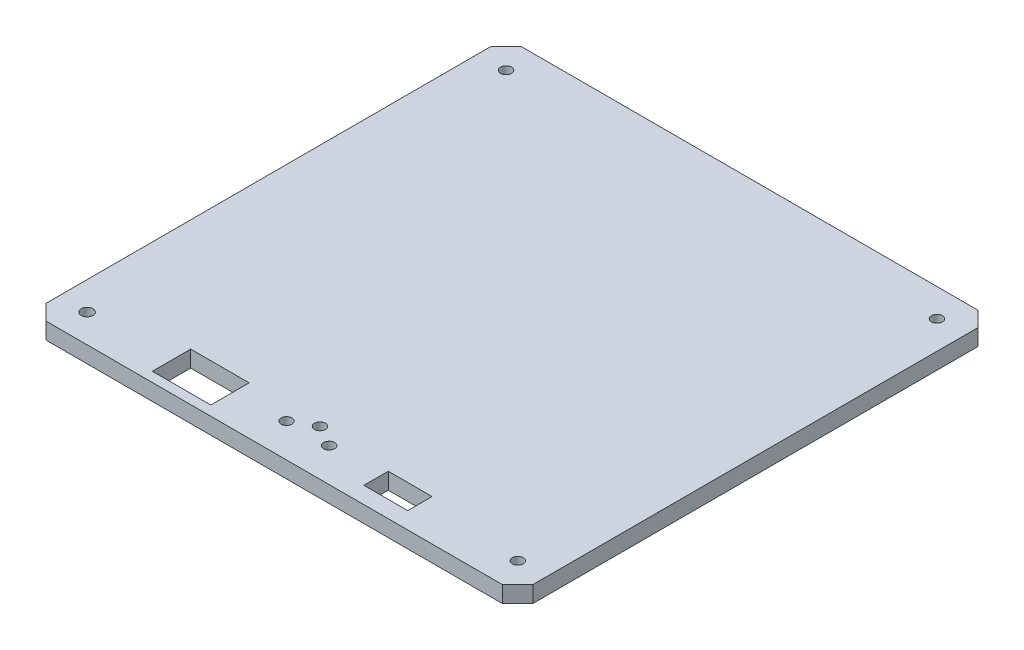
SolidWorks part; units mm, degrees
ref_plane "Front Plane" through (0, 0, 0) normal (0, 0, 1) x (1, 0, 0)
ref_plane "Top Plane" through (0, 0, 0) normal (0, 1, 0) x (1, 0, 0)
ref_plane "Right Plane" through (0, 0, 0) normal (1, 0, 0) x (0, 0, -1)
sketch "Sketch1" plane through (0, 0, 0) normal (0, 1, 0) x (1, 0, 0)
  line L1 (-75.184, -75.184) -> (75.184, -75.184)
  line L2 (-75.184, -75.184) -> (-75.184, 75.184)
  line L3 (-75.184, 75.184) -> (75.184, 75.184)
  line L4 (75.184, -75.184) -> (75.184, 75.184)
  line L5 (-75.184, -75.184) -> (75.184, 75.184) construction
  line L6 (-75.184, 75.184) -> (75.184, -75.184) construction
  point P0 (0, 0)
  dimension "D1" = 150.368
  dimension "D2" = 150.368
extrude "Boss-Extrude1" add sketch "Sketch1" along normal blind 6.858
sketch "Sketch2" plane through (0, 6.858, 0) normal (0, 1, 0) x (1, 0, 0)
  line L1 (-101.6, -99.187) -> (101.6, -99.187)
  line L2 (-101.6, -99.187) -> (-101.6, 99.187)
  line L3 (-101.6, 99.187) -> (101.6, 99.187)
  line L4 (101.6, -99.187) -> (101.6, 99.187)
  line L5 (-101.6, -99.187) -> (101.6, 99.187) construction
  line L6 (-101.6, 99.187) -> (101.6, -99.187) construction
  point P0 (0, 0)
  dimension "D1" = 203.2
  dimension "D2" = 198.374
extrude "Boss-Extrude2" add sketch "Sketch2" against normal blind 6.858
sketch "Sketch4" plane through (0, 6.858, 0) normal (0, 1, 0) x (1, 0, 0)
  circle A0 centre (0.0008, -80.0467) radius 2.286
  dimension "D1" = 4.572
sketch "Sketch5" plane through (0, 6.858, 0) normal (0, 1, 0) x (1, 0, 0)
  circle A0 centre (-8.8892, -85.1267) radius 2.286
  circle A1 centre (8.8908, -85.1267) radius 2.286
extrude "Cut-Extrude2" cut sketch "Sketch5" against normal up to surface (6.858 mm away) up to face at (0, 0, 0)
sketch "Sketch6" plane through (0, 0, 0) normal (0, -1, 0) x (-1, 0, 0)
  line L0 (12.6992, -83.8567) -> (12.6992, -86.3967) construction
  line L1 (-30.4808, -82.0316) -> (-48.7688, -82.0316)
  line L2 (-30.4808, -82.0316) -> (-30.4808, -92.1916)
  line L3 (-30.4808, -92.1916) -> (-48.7688, -92.1916)
  line L4 (-48.7688, -82.0316) -> (-48.7688, -92.1916)
  line L5 (-30.4808, -82.0316) -> (-48.7688, -92.1916) construction
  line L6 (-30.4808, -92.1916) -> (-48.7688, -82.0316) construction
  line L7 (54.8632, -79.1106) -> (30.4792, -79.1106)
  line L8 (54.8632, -79.1106) -> (54.8632, -95.1126)
  line L9 (54.8632, -95.1126) -> (30.4792, -95.1126)
  line L10 (30.4792, -79.1106) -> (30.4792, -95.1126)
  line L11 (54.8632, -79.1106) -> (30.4792, -95.1126) construction
  line L12 (54.8632, -95.1126) -> (30.4792, -79.1106) construction
  line L13 (-12.7008, -86.3967) -> (-12.7008, -83.8567) construction
  point P0 (-39.6248, -87.1116)
  point P5 (42.6712, -87.1116)
  point P10 (42.814, -87.1116)
  point P11 (-38.8513, -87.1116)
  dimension "D1" = 10.16
  dimension "D2" = 18.288
  dimension "D3" = 24.384
  dimension "D4" = 16.002
  dimension "D5" = 17.78
  dimension "D6" = 17.78
extrude "Cut-Extrude3" cut sketch "Sketch6" against normal up to surface (6.858 mm away) up to face at (-8.8892, 6.858, 87.4127)
sketch "Sketch7" plane through (0, 6.858, 0) normal (0, 1, 0) x (1, 0, 0)
  line L0 (-101.6, 99.187) -> (-101.6, 93.0071)
  line L1 (-101.6, 99.187) -> (-101.6, -99.187) construction
  line L2 (-101.6, 93.0071) -> (-95.3395, 99.187)
  line L3 (101.6, 99.187) -> (-101.6, 99.187) construction
  line L4 (-95.2492, 99.2773) -> (-101.5992, 92.9273) construction
  line L5 (-95.3395, 99.187) -> (-101.6, 99.187)
  line L6 (101.6, 99.187) -> (95.3411, 99.187)
  line L7 (101.6008, 92.9273) -> (95.2508, 99.2773) construction
  line L8 (95.3411, 99.187) -> (101.6, 92.9281)
  line L9 (101.6, -99.187) -> (101.6, 99.187) construction
  line L10 (101.6, 92.9281) -> (101.6, 99.187)
  line L11 (101.6, -99.187) -> (95.3411, -99.187)
  line L12 (-101.6, -99.187) -> (101.6, -99.187) construction
  line L13 (95.3411, -99.187) -> (101.6, -92.7475)
  line L14 (95.2508, -99.0967) -> (101.6008, -92.7467) construction
  line L15 (101.6, -92.7475) -> (101.6, -99.187)
  line L16 (-101.6, -99.187) -> (-101.6, -92.7475)
  line L19 (-101.6, -92.7475) -> (-95.18, -99.187)
  line L20 (-101.6, -99.187) -> (-95.18, -99.187)
  point P32 (-95.18, -99.187)
  point P35 (-95.2492, -99.0967)
  point P41 (-95.18, -99.1735)
  line M12 (101.6, -99.187) -> (101.6, 99.187)
  line M15 (-101.6, -99.187) -> (101.6, -99.187)
sketch "Sketch8" plane through (0, 6.858, 0) normal (0, 1, 0) x (1, 0, 0)
  line L0 (-54.8632, -79.1106) -> (-54.8632, -95.1126) construction
  line L1 (-54.8632, -95.1126) -> (-30.4792, -95.1126) construction
  circle A0 centre (-89.8618, -87.3593) radius 2.4503
  circle A1 centre (89.8635, -87.3593) radius 2.286
  circle A2 centre (89.8635, 87.54) radius 2.286
  circle A3 centre (-89.8618, 87.4488) radius 2.286
  dimension "D1" = 4.9006
  dimension "D2" = 4.572
  dimension "D3" = 144.7267
  dimension "D4" = 34.9987
  dimension "D5" = 7.7533
  dimension "D6" = 182.5615
  dimension "D7" = 182.6526
extrude "Cut-Extrude8" cut sketch "Sketch8" against normal up to surface (6.858 mm away) up to face at (39.6248, 0, 87.1116)
extrude "Cut-Extrude10" cut sketch "Sketch7" against normal up to surface (6.858 mm away) contours L13 M15 M12 | L5 L0 L2 | L10 L6 L8 | L19 L20 L16 up to face at (-89.8618, 0, -89.7348)
sketch "Sketch9" plane through (0, 0, 0) normal (0, -1, 0) x (-1, 0, 0)
  line L1 (75.184, 78.8843) -> (-75.184, 78.8843)
  line L2 (75.184, 78.8843) -> (75.184, -71.4837)
  line L3 (75.184, -71.4837) -> (-75.184, -71.4837)
  line L4 (-75.184, 78.8843) -> (-75.184, -71.4837)
  line L5 (75.184, 78.8843) -> (-75.184, -71.4837) construction
  line L6 (75.184, -71.4837) -> (-75.184, 78.8843) construction
  point P0 (0, 13.6102)
  point P7 (0, 13.6102)
  dimension "D1" = 150.368
extrude "Cut-Extrude11" cut sketch "Sketch9" against normal blind 5.08
extrude "Cut-Extrude12" cut sketch "Sketch4" against normal up to surface (6.858 mm away) up to face at (0, 0, -3.7003)
